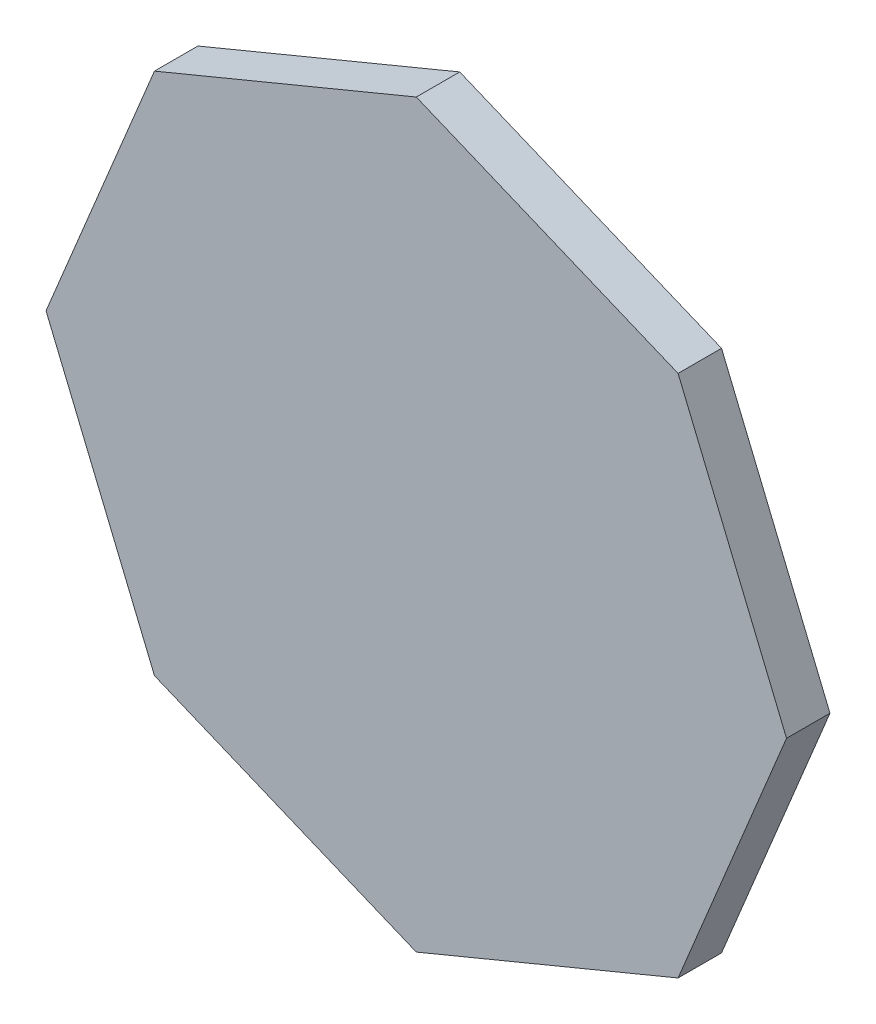
SolidWorks part; units mm, degrees
ref_plane "Front Plane" through (0, 0, 0) normal (0, 0, 1) x (1, 0, 0)
ref_plane "Top Plane" through (0, 0, 0) normal (0, 1, 0) x (1, 0, 0)
ref_plane "Right Plane" through (0, 0, 0) normal (1, 0, 0) x (0, 0, -1)
sketch "Sketch1" plane through (0, 0, 0) normal (0, 0, 1) x (1, 0, 0)
  line L0 (0, 0) -> (0, -195.9844) construction
  line L1 (0, 0) -> (-138.5819, -138.5819) construction
  line L2 (0, 0) -> (-195.9844, 0) construction
  line L3 (0, 0) -> (-138.5819, 138.5819) construction
  line L4 (0, 0) -> (0, 195.9844) construction
  line L5 (0, 0) -> (138.5819, 138.5819) construction
  line L6 (0, 0) -> (195.9844, 0) construction
  line L7 (0, 0) -> (138.5819, -138.5819) construction
  line L8 (0, 195.9844) -> (-138.5819, 138.5819)
  line L9 (-138.5819, 138.5819) -> (-195.9844, 0)
  line L10 (-195.9844, 0) -> (-138.5819, -138.5819)
  line L11 (-138.5819, -138.5819) -> (0, -195.9844)
  line L12 (0, -195.9844) -> (138.5819, -138.5819)
  line L13 (138.5819, -138.5819) -> (195.9844, 0)
  line L14 (195.9844, 0) -> (138.5819, 138.5819)
  line L15 (138.5819, 138.5819) -> (0, 195.9844)
  circle A0 centre (0, 0) radius 195.9844 construction
  point P13 (0, 0)
  dimension "D2" = 150
  dimension "D1" = 8
extrude "Boss-Extrude1" add sketch "Sketch1" along normal blind 3
sketch "Sketch5" plane through (-69.291, -167.2832, 0) normal (-0.3827, -0.9239, 0) x (0.9239, -0.3827, 0)
  line L1 (75, 0) -> (75, -20)
  line L2 (-75, 0) -> (-75, -20)
  line L3 (75, -20) -> (-75, -20)
  line L4 (-125, 35.4266) -> (-75, -20) construction
  line L5 (-125, 35.4266) -> (75, -20) construction
  line L6 (75, 0) -> (-75, 0)
  line L7 (-75, 3) -> (-75, 0) construction
  line L8 (-75, 0) -> (75, 0) construction
  line L9 (75, 3) -> (75, 0) construction
  point P1 (-125, 35.4266)
  dimension "D1" = 20
  dimension "D2" = 20
extrude "Boss-Extrude2" add sketch "Sketch5" against normal blind 3
mirror "Mirror1" about plane through (0, 0, 0) normal (0, 1, 0) of "Boss-Extrude2"
mirror "Mirror2" about plane through (0, 0, 0) normal (1, 0, 0) of "Mirror1", "Boss-Extrude2"
sketch "Sketch6" plane through (-167.2832, -69.291, 0) normal (-0.9239, -0.3827, 0) x (0, 0, 1)
  line L0 (3, 75) -> (0, 75) construction
  line L1 (3, -75) -> (-20, -75)
  line L2 (3, -75) -> (3, 75)
  line L3 (3, 75) -> (-20, 75)
  line L4 (-20, -75) -> (-20, 75)
  dimension "D1" = 23
extrude "Boss-Extrude3" add sketch "Sketch6" against normal blind 3
mirror "Mirror3" about plane through (0, 0, 0) normal (0, 1, 0) of "Boss-Extrude3"
mirror "Mirror4" about plane through (0, 0, 0) normal (1, 0, 0) of "Boss-Extrude1", "Mirror3"
fillet "Fillet1" radius 2 8 edges at (68.1429, 164.5115, 0) (-68.1429, 164.5115, 0) (-164.5115, 68.1429, 0) (-164.5115, -68.1429, 0) (-68.1429, -164.5115, 0) (68.1429, -164.5115, 0) (164.5115, 68.1429, 0) (164.5115, -68.1429, 0)
